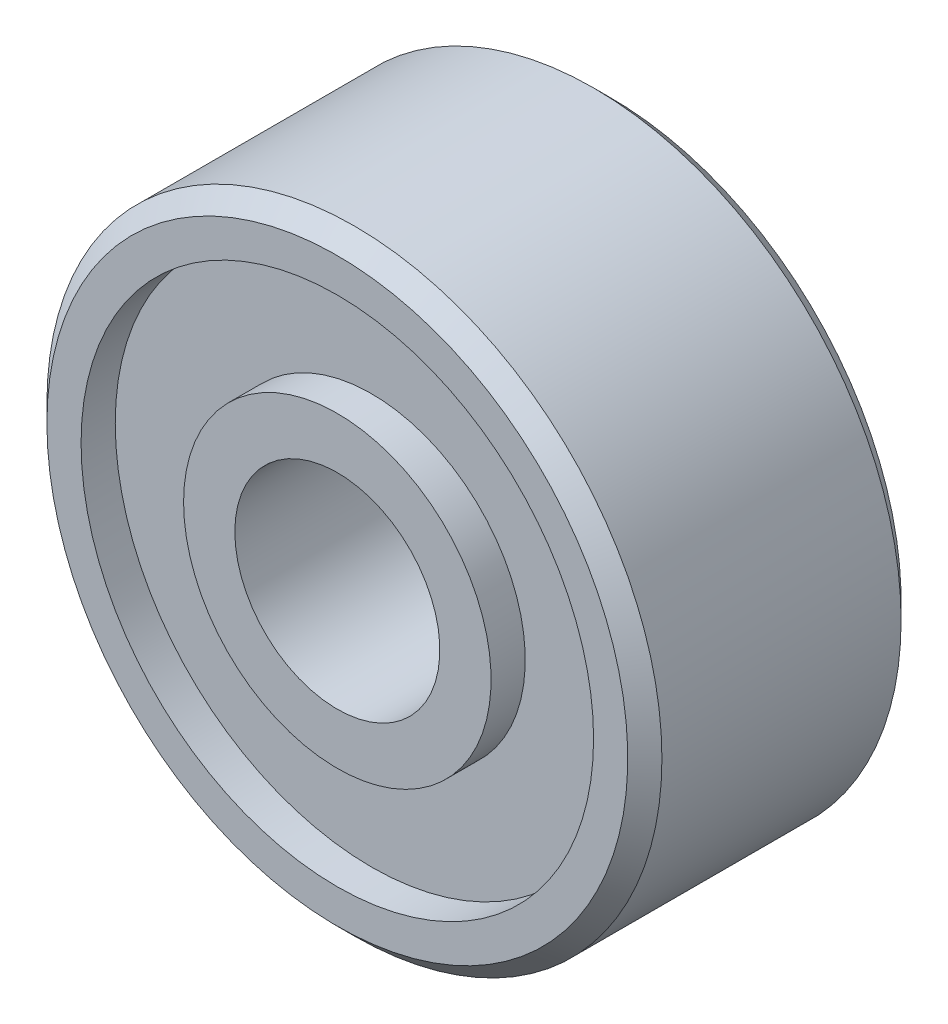
SolidWorks part; units mm, degrees
ref_plane "Front Plane" through (0, 0, 0) normal (0, 0, 1) x (1, 0, 0)
ref_plane "Top Plane" through (0, 0, 0) normal (0, 1, 0) x (1, 0, 0)
ref_plane "Right Plane" through (0, 0, 0) normal (1, 0, 0) x (0, 0, -1)
ref_plane "Plane1" through (0, 0, 0) normal (0, -1, 0) x (1, 0, 0)
sketch "Sketch1" plane through (0, 0, 0) normal (0, -1, 0) x (1, 0, 0)
  line L0 (4.5, 1.25) -> (4.25, 1.5)
  line L1 (4.25, 1.5) -> (3.75, 1.5)
  line L2 (3.75, 1.5) -> (3.75, 1)
  line L3 (3.75, 1) -> (2.25, 1)
  line L4 (2.25, 1) -> (2.25, 1.5)
  line L5 (2.25, 1.5) -> (1.5, 1.5)
  line L6 (1.5, 1.5) -> (1.5, -2.5)
  line L7 (1.5, -2.5) -> (2.25, -2.5)
  line L8 (2.25, -2.5) -> (2.25, -2)
  line L9 (2.25, -2) -> (3.75, -2)
  line L10 (3.75, -2) -> (3.75, -2.5)
  line L11 (3.75, -2.5) -> (4.25, -2.5)
  line L12 (4.25, -2.5) -> (4.5, -2.25)
  line L13 (4.5, -2.25) -> (4.5, 1.25)
  line L14 (0, 2.5) -> (0, -2.5) construction
  dimension "D1" = 3
  dimension "D2" = 0.25
  dimension "D3" = 4.5
  dimension "D4" = 4
  dimension "D5" = 9
  dimension "D7" = 0.5
  dimension "D8" = 45
  dimension "D9" = 7.5
revolve "Revolve1" add sketch "Sketch1" angle 360 about L14
